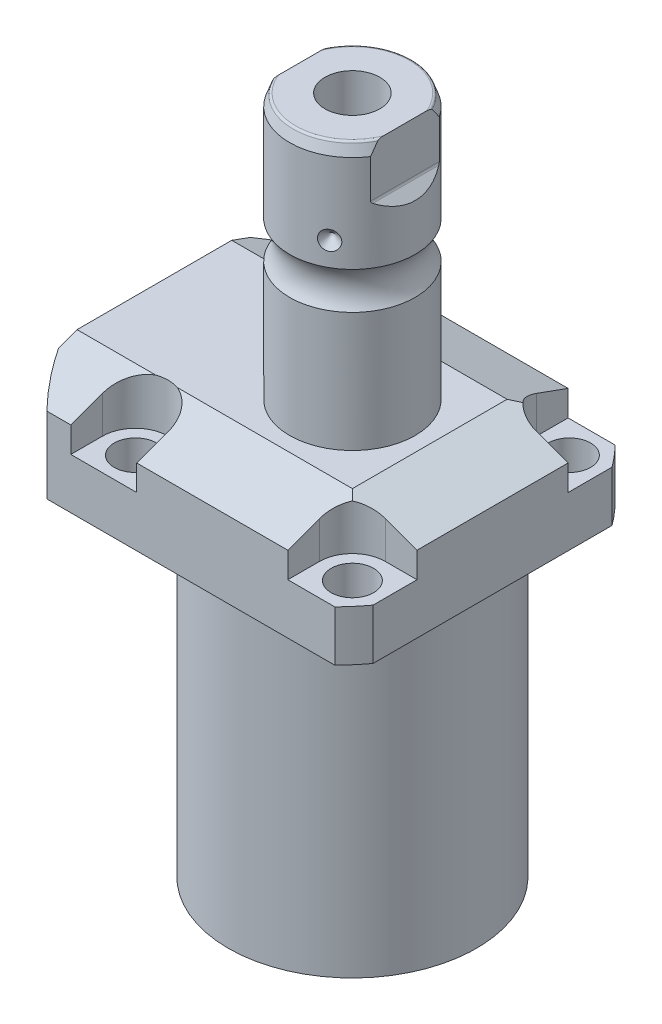
SolidWorks part; units mm, degrees
material "Alloy Steel"
ref_plane "Front Plane" through (0, 0, 0) normal (0, 0, 1) x (1, 0, 0)
ref_plane "Top Plane" through (0, 0, 0) normal (0, 1, 0) x (1, 0, 0)
ref_plane "Right Plane" through (0, 0, 0) normal (1, 0, 0) x (0, 0, -1)
sketch "Sketch1" plane through (0, 0, 0) normal (0, -1, 0) x (0, 0, 1)
  line L0 (-35.433, 50.063) -> (35.433, 50.063)
  line L1 (35.433, 50.063) -> (35.433, -35.433)
  line L2 (35.433, -35.433) -> (-35.433, -35.433)
  line L3 (-35.433, -35.433) -> (-35.433, 50.063)
  line L4 (0, 0) -> (0, -60.6467) construction
  dimension "D1" = 35.433
  dimension "D2" = 85.496
  dimension "D3" = 70.866
extrude "Extrude1" add sketch "Sketch1" against normal blind 104.521
sketch "Sketch2" plane through (0, 0, 0) normal (0, -1, 0) x (1, 0, 0)
  circle A0 centre (-5.4102, 0) radius 50.8
  dimension "D1" = 101.6
  dimension "D2" = 5.4102
extrude "Cut-Extrude1" cut sketch "Sketch2" against normal through all flip side to cut
sketch "Sketch3" plane through (0, 0, 0) normal (1, 0, 0) x (0, 0, -1)
  line L0 (31.3945, 0) -> (31.3945, 79.502)
  line L1 (31.3945, 79.502) -> (76.5937, 79.502)
  line L2 (76.5937, 79.502) -> (76.5937, 0)
  line L3 (76.5937, 0) -> (31.3945, 0)
  line L4 (0, -93.345) -> (0, 4.445) construction
  line L5 (24.2233, 0) -> (-24.2233, 0) construction
  dimension "D1" = 62.789
  dimension "D2" = 153.1874
  dimension "D3" = 79.502
revolve "Cut-Revolve1" cut sketch "Sketch3" angle 360 about L4
fillet "Fillet1" radius 0.381 1 edges at (0, 79.502, -31.3945)
sketch "Sketch4" plane through (0, 104.521, 0) normal (0, 1, 0) x (-1, 0, 0)
  line L0 (-35.433, -30.2072) -> (-35.433, 30.2072) construction
  line L1 (41.8127, 35.433) -> (-30.9923, 35.433) construction
  line L2 (-19.1008, -35.433) -> (-19.1008, -27.432)
  line L3 (-35.433, -35.433) -> (-19.1008, -35.433)
  line L4 (-35.433, -19.1008) -> (-35.433, -35.433)
  line L5 (-27.432, -19.1008) -> (-35.433, -19.1008)
  line L6 (35.7632, -35.433) -> (19.1008, -35.433)
  line L7 (19.1008, 35.433) -> (19.1008, 27.432)
  line L8 (35.7632, 35.433) -> (35.7632, 27.432)
  line L9 (35.7632, 35.433) -> (19.1008, 35.433)
  line L10 (-27.432, 19.1008) -> (-35.433, 19.1008)
  line L11 (-35.433, 19.1008) -> (-35.433, 35.433)
  line L12 (-35.433, 35.433) -> (-19.1008, 35.433)
  line L13 (-19.1008, 35.433) -> (-19.1008, 27.432)
  line L14 (-48.9217, 0) -> (49.4551, 0) construction
  line L15 (35.7632, -35.433) -> (35.7632, -27.432)
  line L16 (19.1008, -35.433) -> (19.1008, -27.432)
  arc A0 (19.1008, -27.432) -> (35.7632, -27.432) centre (27.432, -27.432) cw
  arc A1 (-27.432, -19.1008) -> (-19.1008, -27.432) centre (-27.432, -27.432) cw
  arc A2 (-27.432, 19.1008) -> (-19.1008, 27.432) centre (-27.432, 27.432) ccw
  arc A3 (19.1008, 27.432) -> (35.7632, 27.432) centre (27.432, 27.432) ccw
  dimension "D2" = 8.3312
  dimension "D1" = 27.432
  dimension "D3" = 27.432
  dimension "D4" = 54.864
extrude "Cut-Extrude2" cut sketch "Sketch4" against normal blind 12.243
sketch "Sketch5" plane through (0, 0, 0) normal (1, 0, 0) x (0, 0, -1)
  line L0 (-19.558, 104.521) -> (-35.433, 98.743)
  line L1 (0, 0) -> (0, 154.1081) construction
  line L2 (-19.558, 104.521) -> (-35.433, 104.521)
  line L3 (-35.433, 104.521) -> (-35.433, 98.743)
  dimension "D1" = 15.875
  dimension "D2" = 20
extrude "Cut-Extrude9" cut sketch "Sketch5" against normal through all and the other way through all
mirror "Mirror1" about plane through (0, 0, 0) normal (0, 0, 1) of "Cut-Extrude9"
sketch "Sketch9" plane through (0, 0, 0) normal (0, 0, 1) x (1, 0, 0)
  line L0 (19.558, 104.521) -> (35.433, 98.743)
  line L1 (35.433, 98.743) -> (35.433, 104.521)
  line L2 (35.433, 104.521) -> (19.558, 104.521)
  dimension "D1" = 15.875
  dimension "D2" = 20
extrude "Cut-Extrude7" cut sketch "Sketch9" against normal through all and the other way through all
ref_plane "Plane14" through (-35.0774, 0, 0) normal (1, 0, 0) x (0, 0, -1)
sketch "Sketch20" plane through (-35.0774, 88.9, -18.1102) normal (1, 0, 0) x (0, 1, 0)
  line L0 (-88.9, 18.1102) -> (39.8401, 18.1102) construction
  line L1 (-7.2797, 32.639) -> (36.9042, 32.639) construction
  line L2 (-9.398, 38.3413) -> (-7.9502, 38.3413)
  line L3 (-9.398, -6.1131) -> (-9.398, 42.3335) construction
  line L4 (-7.9502, 38.3413) -> (-7.9502, 35.8902)
  line L5 (-7.9502, 35.8902) -> (-6.9342, 35.8902)
  line L6 (-6.9342, 35.8902) -> (-6.9342, 33.8836)
  line L7 (-6.9342, 33.8836) -> (4.0386, 33.8836)
  line L8 (4.0386, 33.8836) -> (4.0386, 32.639)
  line L9 (4.0386, 32.639) -> (-9.398, 32.639)
  line L10 (-9.398, 38.3413) -> (-9.398, 32.639)
  dimension "D1" = 14.5288
  dimension "D2" = 11.4046
  dimension "D3" = 1.4478
  dimension "D4" = 6.5024
  dimension "D5" = 1.016
  dimension "D6" = 2.4892
  dimension "D7" = 10.9728
revolve "Cut-Revolve4" cut sketch "Sketch20" angle 360 about L1
mirror "Mirror10" about plane through (0, 0, 0) normal (0, 0, 1) of "Cut-Revolve4"
sketch "Sketch10" plane through (-35.0774, 88.9, -18.1102) normal (1, 0, 0) x (0, 1, 0)
  line L0 (-1.0325, 3.5814) -> (1.5659, 3.5814) construction
  line L1 (4.0386, 4.826) -> (-6.9342, 4.826) construction
  line L2 (-6.9342, 2.3368) -> (4.0386, 2.3368) construction
  line L4 (-9.398, -12.097) -> (-9.398, 48.3174) construction
  circle A0 centre (-9.1313, 8.1026) radius 1.1811
  dimension "D1" = 2.3622
  dimension "D2" = 0.2667
  dimension "D3" = 9.0424
revolve "Revolve4" add sketch "Sketch10" angle 360 about L0
mirror "Mirror12" about plane through (0, 0, 0) normal (0, 0, 1) of bodies 135
sketch "Sketch15" plane through (0, 0, 0) normal (1, 0, 0) x (0, 0, -1)
  line L0 (0, 104.521) -> (15.875, 104.521)
  line L1 (15.875, 104.521) -> (15.875, 134.7639)
  line L2 (15.875, 144.1781) -> (15.875, 168.656)
  line L3 (14.8118, 171.577) -> (0, 171.577)
  line L4 (0, 171.577) -> (0, 104.521)
  line L5 (0, 250.2908) -> (0, 28.9095) construction
  line L6 (19.558, 104.521) -> (-19.558, 104.521) construction
  line L7 (14.8118, 171.577) -> (15.875, 168.656)
  line L8 (-31.3945, 0) -> (31.3945, 0) construction
  arc A0 (15.875, 144.1781) -> (15.875, 134.7639) centre (22.2504, 139.471) ccw
  dimension "D2" = 20
  dimension "D4" = 7.9248
  dimension "D6" = 28.6512
  dimension "D1" = 171.577
  dimension "D3" = 31.75
  dimension "D5" = 32.106
  dimension "D7" = 2.921
revolve "Revolve3" add sketch "Sketch15" angle 360 about L5
hole_wizard "Hole1" positions "Sketch18" profile "Sketch17" legacy end condition up to next
sketch "Sketch18" plane through (0, 92.278, 0) normal (0, 1, 0) x (-1, 0, 0)
  arc A0 (35.7632, -27.432) -> (19.1008, -27.432) centre (27.432, -27.432) ccw construction
  arc A1 (19.1008, 27.432) -> (35.7632, 27.432) centre (27.432, 27.432) ccw construction
  arc A2 (-27.432, 19.1008) -> (-19.1008, 27.432) centre (-27.432, 27.432) ccw construction
  arc A3 (-19.1008, -27.432) -> (-27.432, -19.1008) centre (-27.432, -27.432) ccw construction
  point P0 (-27.432, -27.432)
  point P1 (-27.432, 27.432)
  point P3 (27.432, 27.432)
  point P5 (27.432, -27.432)
sketch "Sketch17" plane through (27.432, 92.278, -27.432) normal (1, 0, 0) x (0, 0, 1)
  line L0 (0, 0) -> (0, 12.776)
  line L1 (0, 12.776) -> (5.3594, 12.776)
  line L2 (5.3594, 12.776) -> (5.3594, 0)
  line L3 (5.3594, 0) -> (0, 0)
  line L4 (0, 110) -> (0, -10) construction
  dimension "Diameter" = 10.7188
  dimension "Depth" = 12.776
chamfer "Chamfer1" distance 0.635 angle 45 2 edges at (-35.0774, 81.9658, 13.2842) (-35.0774, 81.9658, -13.2842)
ref_plane "Plane15" through (0, 92.5068, 0) normal (0, -1, 0) x (1, 0, 0)
sketch "Sketch21" plane through (0, 92.5068, 0) normal (0, -1, 0) x (1, 0, 0)
  line L0 (-57.5495, -12.9794) -> (-2.9353, -12.9794) construction
  line L1 (-50.063, -1.9304) -> (-49.809, -1.9304)
  line L2 (-49.809, -1.9304) -> (-49.809, -6.3246)
  line L3 (-49.809, -6.3246) -> (-49.0978, -7.0358)
  line L4 (-49.0978, -7.0358) -> (-35.6358, -7.0358)
  line L5 (-35.6358, -7.0358) -> (-35.6358, -12.9794)
  line L6 (-35.6358, -12.9794) -> (-50.063, -12.9794)
  line L7 (-50.063, 24.2233) -> (-50.063, -24.2233) construction
  line L8 (-50.063, -12.9794) -> (-50.063, -1.9304)
  dimension "D1" = 12.9794
  dimension "D2" = 0.254
  dimension "D3" = 22.098
  dimension "D4" = 45
  dimension "D5" = 0.7112
  dimension "D6" = 11.8872
  dimension "D7" = 14.1732
revolve "Cut-Revolve5" cut sketch "Sketch21" angle 360 about L0
mirror "Mirror13" about plane through (0, 0, 0) normal (0, 0, 1) of "Cut-Revolve5"
fillet "Fillet2" radius 0.635 1 edges at (0, 171.577, 14.8118)
sketch "Sketch26" plane through (0, 0, 0) normal (0, 0, 1) x (1, 0, 0)
  line L0 (-39.772, 150.159) -> (35.3173, 150.159) construction
  line L1 (-15.875, 152.572) -> (-13.462, 150.159)
  line L2 (-15.875, 168.656) -> (-15.875, 144.1781) construction
  line L3 (-13.462, 150.159) -> (-15.875, 150.159)
  line L4 (-15.875, 150.159) -> (-15.875, 152.572)
  arc A0 (-15.875, 134.7639) -> (-15.875, 144.1781) centre (-22.2504, 139.471) ccw construction
  dimension "D1" = 45
  dimension "D2" = 4.826
  dimension "D3" = 10.688
revolve "Cut-Revolve7" cut sketch "Sketch26" angle 360 about L0
pattern_circular "CirPattern1" count 3 over 360 about axis through (0, 250.2908, 0) along (0, 1, 0) of "Cut-Revolve7"
hole_wizard "Hole2" positions "Sketch28" profile "Sketch27" legacy
sketch "Sketch28" plane through (0, 171.577, 0) normal (0, 1, 0) x (-1, 0, 0)
  circle A0 centre (0, 0) radius 15.875 construction
  point P0 (0, 0)
sketch "Sketch27" plane through (0, 171.577, 0) normal (1, 0, 0) x (0, 0, 1)
  line L0 (0, 0) -> (0, 29.5665)
  line L1 (0, 29.5665) -> (6.9342, 25.4)
  line L2 (6.9342, 25.4) -> (6.9342, 0)
  line L4 (6.9342, 0) -> (0, 0)
  line L6 (0, 29.5665) -> (-6.9342, 25.4) construction
  line L7 (0, -4.2442) -> (0, 117.3081) construction
  dimension "Diameter" = 13.8684
  dimension "Depth" = 25.4
  dimension "Drill Angle" = 118
sketch "Sketch29" plane through (0, 0, 0) normal (0, 0, 1) x (1, 0, 0)
  line L0 (0, 0) -> (0, 192.0172) construction
  line L1 (13.284, 171.577) -> (13.284, 158.877)
  line L2 (14.3672, 171.577) -> (-14.3672, 171.577) construction
  line L3 (13.5072, 158.3382) -> (15.875, 155.9704)
  line L5 (15.875, 155.9704) -> (15.875, 171.577)
  line L6 (15.875, 171.577) -> (13.284, 171.577)
  line L7 (-15.875, 171.577) -> (-13.284, 171.577)
  line L8 (-15.875, 155.9704) -> (-15.875, 171.577)
  line L9 (-13.5072, 158.3382) -> (-15.875, 155.9704)
  line L10 (-13.284, 171.577) -> (-13.284, 158.877)
  arc A0 (13.284, 158.877) -> (13.5072, 158.3382) centre (14.046, 158.877) ccw
  arc A1 (-13.284, 158.877) -> (-13.5072, 158.3382) centre (-14.046, 158.877) cw
  dimension "D2" = 0.762
  dimension "D1" = 45
  dimension "D3" = 26.568
  dimension "D4" = 12.7
extrude "Cut-Extrude10" cut sketch "Sketch29" against normal through all and the other way through all
